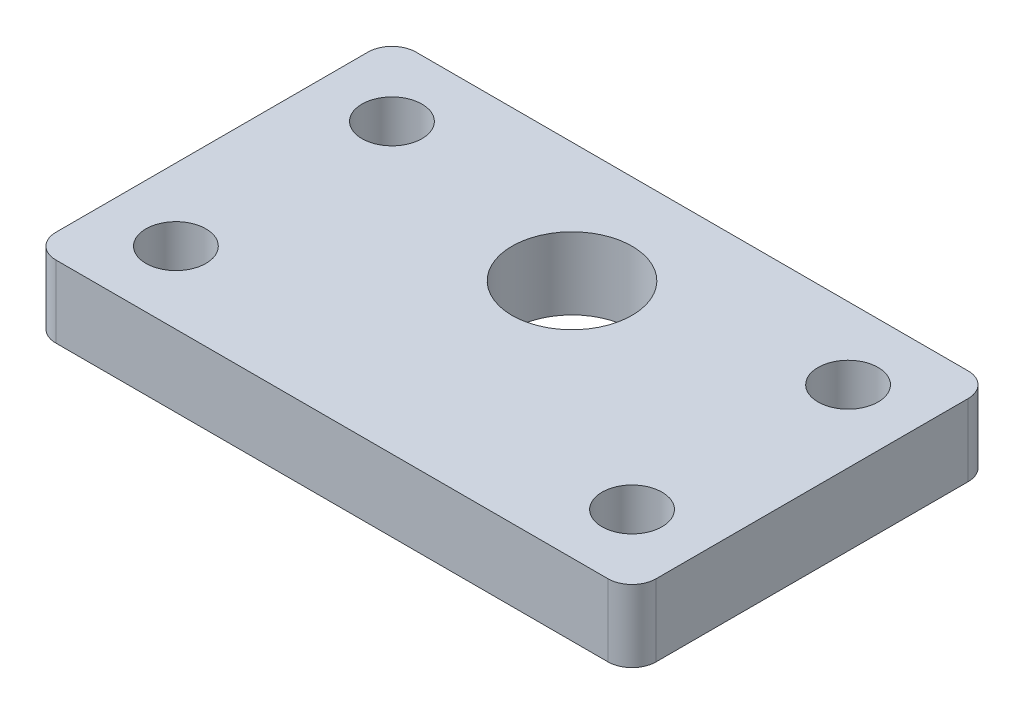
SolidWorks part; units mm, degrees
ref_plane "Front Plane" through (0, 0, 0) normal (0, 0, 1) x (1, 0, 0)
ref_plane "Top Plane" through (0, 0, 0) normal (0, 1, 0) x (1, 0, 0)
ref_plane "Right Plane" through (0, 0, 0) normal (1, 0, 0) x (0, 0, -1)
sketch "Sketch1" plane through (0, 0, 0) normal (0, 1, 0) x (1, 0, 0)
  line L1 (115, -75) -> (-115, -75)
  line L2 (125, -65) -> (125, 65)
  line L3 (115, 75) -> (-115, 75)
  line L4 (-125, -65) -> (-125, 65)
  line L5 (125, -75) -> (-125, 75) construction
  line L6 (125, 75) -> (-125, -75) construction
  arc A0 (-115, -75) -> (-125, -65) centre (-115, -65) cw
  arc A1 (125, 65) -> (115, 75) centre (115, 65) ccw
  arc A2 (115, -75) -> (125, -65) centre (115, -65) ccw
  arc A3 (-115, 75) -> (-125, 65) centre (-115, 65) ccw
  point P0 (0, 0)
  dimension "D3" = 10
  dimension "D1" = 250
  dimension "D2" = 150
extrude "Boss-Extrude1" add sketch "Sketch1" along normal blind 30
sketch "Sketch2" plane through (0, 30, 0) normal (0, 1, 0) x (1, 0, 0)
  line L0 (115, 75) -> (-115, 75) construction
  line L1 (-125, 65) -> (-125, -65) construction
  circle A0 centre (0, 25) radius 25
  circle A1 centre (-95, 45) radius 12.5
  circle A2 centre (95, 45) radius 12.5
  circle A3 centre (95, -45) radius 12.5
  circle A4 centre (-95, -45) radius 12.5
  dimension "D1" = 50
  dimension "D3" = 25
  dimension "D2" = 50
  dimension "D4" = 30
  dimension "D5" = 30
  dimension "D6" = 2
  dimension "D7" = 2
extrude "Cut-Extrude1" cut sketch "Sketch2" against normal through all
